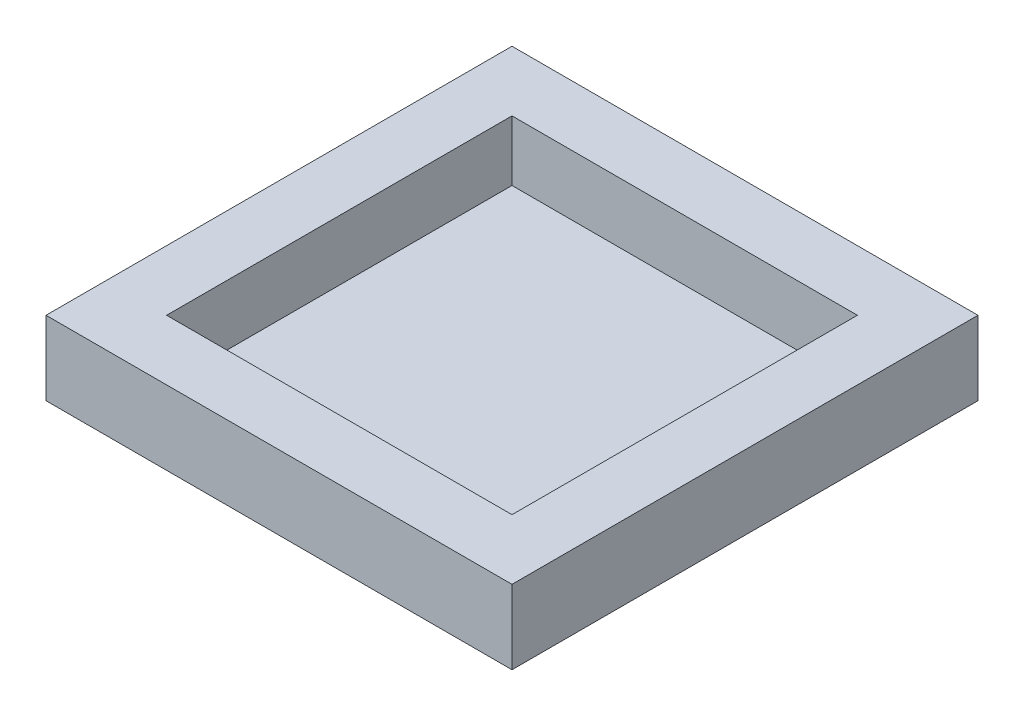
SolidWorks part; units mm, degrees
ref_plane "Plan de face" through (0, 0, 0) normal (0, 0, 1) x (1, 0, 0)
ref_plane "Plan de dessus" through (0, 0, 0) normal (0, 1, 0) x (1, 0, 0)
ref_plane "Plan de droite" through (0, 0, 0) normal (1, 0, 0) x (0, 0, -1)
sketch "Esquisse1" plane through (0, 0, 0) normal (0, 1, 0) x (1, 0, 0)
  line L1 (0, 0) -> (170, 0)
  line L2 (0, 0) -> (0, 170)
  line L3 (0, 170) -> (170, 170)
  line L4 (170, 0) -> (170, 170)
  dimension "D1" = 170
  dimension "D2" = 170
extrude "Extrusion1" add sketch "Esquisse1" along normal blind 5
sketch "Esquisse2" plane through (0, 5, 0) normal (0, 1, 0) x (-1, 0, 0)
  line L1 (0, -170) -> (-170, -170)
  line L2 (0, -170) -> (0, 0)
  line L3 (0, 0) -> (-170, 0)
  line L4 (-170, -170) -> (-170, 0)
  line L5 (-22, -148) -> (-148, -148)
  line L6 (-22, -148) -> (-22, -22)
  line L7 (-22, -22) -> (-148, -22)
  line L8 (-148, -148) -> (-148, -22)
  dimension "D1" = 22
  dimension "D2" = 22
  dimension "D3" = 22
  dimension "D4" = 22
extrude "Extrusion2" add sketch "Esquisse2" along normal blind 22
